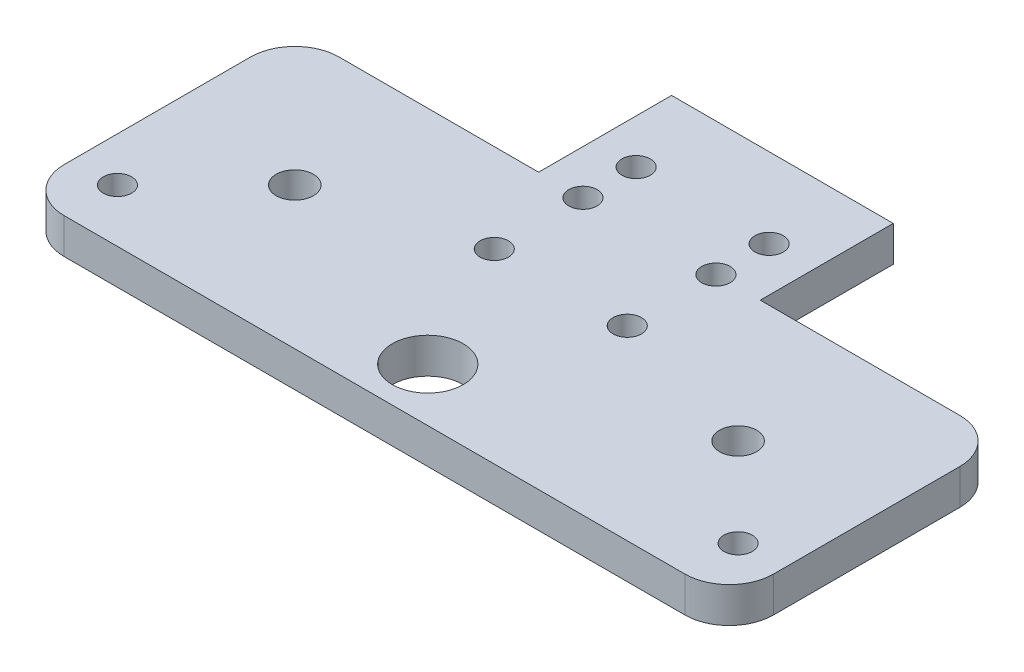
SolidWorks part; units mm, degrees
ref_plane "Front Plane" through (0, 0, 0) normal (0, 0, 1) x (1, 0, 0)
ref_plane "Top Plane" through (0, 0, 0) normal (0, 1, 0) x (1, 0, 0)
ref_plane "Right Plane" through (0, 0, 0) normal (1, 0, 0) x (0, 0, -1)
sketch "Sketch1" plane through (0, 0, 0) normal (0, 1, 0) x (1, 0, 0)
  line L0 (-35, 0) -> (35, 0) construction
  line L1 (-7.5, 5) -> (7.5, 5) construction
  line L2 (-7.5, 5) -> (-7.5, -5) construction
  line L3 (-7.5, -5) -> (7.5, -5) construction
  line L4 (7.5, 5) -> (7.5, -5) construction
  line L5 (0, -5) -> (0, 5) construction
  line L6 (-7.5, 0) -> (7.5, 0) construction
  line L7 (-7.5, 5) -> (7.5, 5) construction
  line L8 (-7.5, 5) -> (-7.5, 11) construction
  line L9 (-7.5, 11) -> (7.5, 11) construction
  line L10 (7.5, 5) -> (7.5, 11) construction
  line L11 (0, 11) -> (0, 5) construction
  line L12 (-7.5, 8) -> (7.5, 8) construction
  line L13 (-35, -26) -> (35, -26)
  line L14 (-35, 0) -> (35, 0) construction
  line L15 (-35, 0) -> (-35, -20) construction
  line L16 (-35, -20) -> (35, -20) construction
  line L17 (35, 0) -> (35, -20) construction
  line L18 (0, -20) -> (0, 0) construction
  line L19 (-35, -10) -> (35, -10) construction
  line L20 (40, -21) -> (40, 0)
  line L21 (35, 5) -> (12.5, 5)
  line L22 (12.5, 5) -> (12.5, 20)
  line L23 (12.5, 20) -> (-12.5, 20)
  line L24 (-12.5, 20) -> (-12.5, 5)
  line L25 (-12.5, 5) -> (-35, 5)
  line L26 (-40, 0) -> (-40, -21)
  circle A0 centre (-7.5, 11) radius 1.6
  circle A1 centre (7.5, 11) radius 1.6
  circle A2 centre (-7.5, -5) radius 1.6
  circle A3 centre (7.5, -5) radius 1.6
  circle A4 centre (-7.5, 5) radius 1.6
  circle A5 centre (7.5, 5) radius 1.6
  circle A6 centre (-35, -20) radius 1.6
  circle A7 centre (35, -20) radius 1.6
  arc A8 (35, -26) -> (40, -21) centre (35, -21) ccw
  arc A9 (40, 0) -> (35, 5) centre (35, 0) ccw
  arc A10 (-35, 5) -> (-40, 0) centre (-35, 0) ccw
  arc A11 (-40, -21) -> (-35, -26) centre (-35, -21) ccw
  circle A12 centre (-25, -10) radius 2.1
  circle A13 centre (25, -10) radius 2.1
  circle A14 centre (0, -20) radius 4
  point P0 (0, 0)
  point P16 (0, 0)
  point P37 (40, -10.5)
  point P40 (0, 20)
  point P164 (0, 8)
  point P375 (0, -10)
  dimension "D4" = 3.2
  dimension "D14" = 4.2
  dimension "D16" = 8
  dimension "D1" = 10
  dimension "D2" = 15
  dimension "D3" = 6
  dimension "D5" = 70
  dimension "D6" = 20
  dimension "D7" = 6
  dimension "D8" = 5
  dimension "D9" = 5
  dimension "D10" = 5
  dimension "D11" = 5
  dimension "D12" = 15
  dimension "D13" = 25
  dimension "D15" = 50
extrude "Boss-Extrude1" add sketch "Sketch1" along normal blind 4
